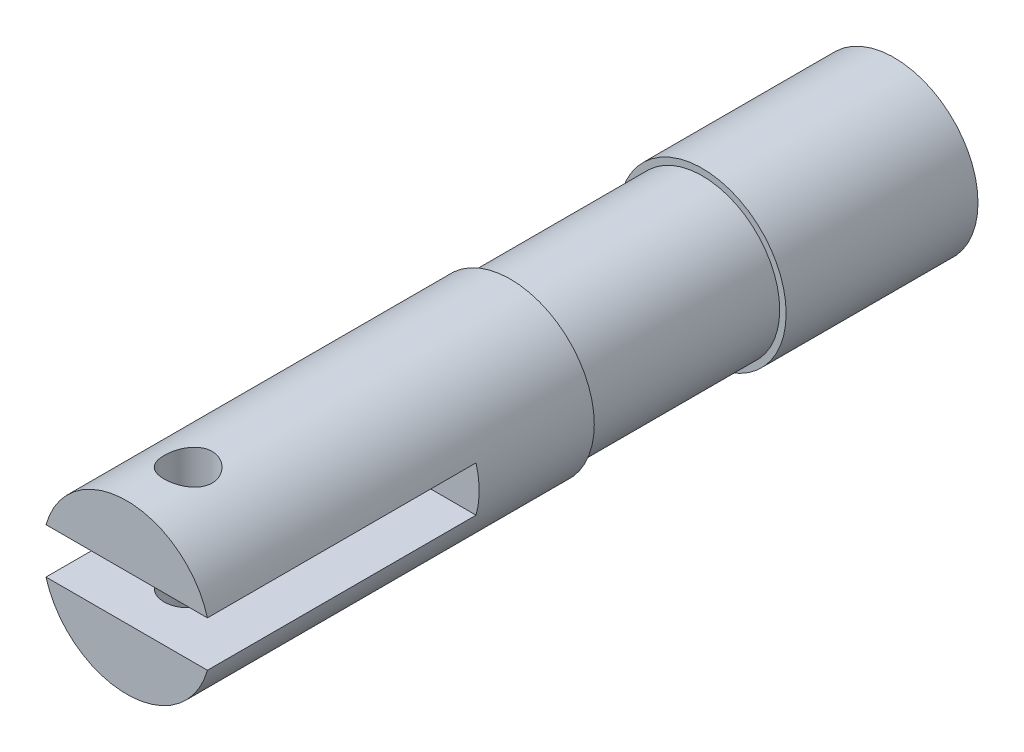
SolidWorks part; units mm, degrees
ref_plane "Front Plane" through (0, 0, 0) normal (0, 0, 1) x (1, 0, 0)
ref_plane "Top Plane" through (0, 0, 0) normal (0, 1, 0) x (1, 0, 0)
ref_plane "Right Plane" through (0, 0, 0) normal (1, 0, 0) x (0, 0, -1)
sketch "Sketch1" plane through (0, 0, 0) normal (0, 0, 1) x (1, 0, 0)
  circle A0 centre (0, 0) radius 5.5499
extrude "Boss-Extrude1" add sketch "Sketch1" along normal blind 38.1
ref_plane "Plane1" through (0, 0, 38.1) normal (0, 0, 1) x (1, 0, 0)
sketch "Sketch2" plane through (0, 0, 38.1) normal (0, 0, 1) x (1, 0, 0)
  line L0 (0, 0) -> (0, 1.5) construction
  line L1 (0, 0) -> (-5.5499, 0) construction
  line L2 (5.3434, 1.5) -> (-5.3434, 1.5)
  line L3 (5.3434, -1.5) -> (-5.3434, -1.5)
  circle A0 centre (0, 0) radius 5.5499 construction
  arc A1 (-5.3434, 1.5) -> (-5.3434, -1.5) centre (0, 0) ccw
  arc A2 (5.3434, -1.5) -> (5.3434, 1.5) centre (0, 0) ccw
extrude "Cut-Extrude1" cut sketch "Sketch2" against normal blind 17.78
ref_plane "Plane2" through (0, -1.5, 0) normal (0, 1, 0) x (1, 0, 0)
sketch "Sketch3" plane through (0, -1.5, 0) normal (0, 1, 0) x (1, 0, 0)
  line L0 (0, -38.1) -> (0, -34.036) construction
  line L1 (-2.2274, -38.1) -> (2.2274, -38.1) construction
  circle A0 centre (0, -34.036) radius 1.5875
extrude "Cut-Extrude2" cut sketch "Sketch3" against normal through all both and the other way through all
sketch "Sketch4" plane through (0, 0, 0) normal (0, 0, 1) x (1, 0, 0)
  circle A0 centre (0, 0) radius 5.5499
extrude "Boss-Extrude4" add sketch "Sketch4" against normal blind 12.7
sketch "Sketch5" plane through (0, -1.5, 0) normal (0, 1, 0) x (1, 0, 0)
sketch "Sketch6" plane through (0, 0, 0) normal (0, 0, 1) x (1, 0, 0)
  circle A0 centre (0, 0) radius 5.5499
  circle A1 centre (0, 0) radius 5.1239
extrude "Cut-Extrude4" cut sketch "Sketch6" along normal blind 12.7
